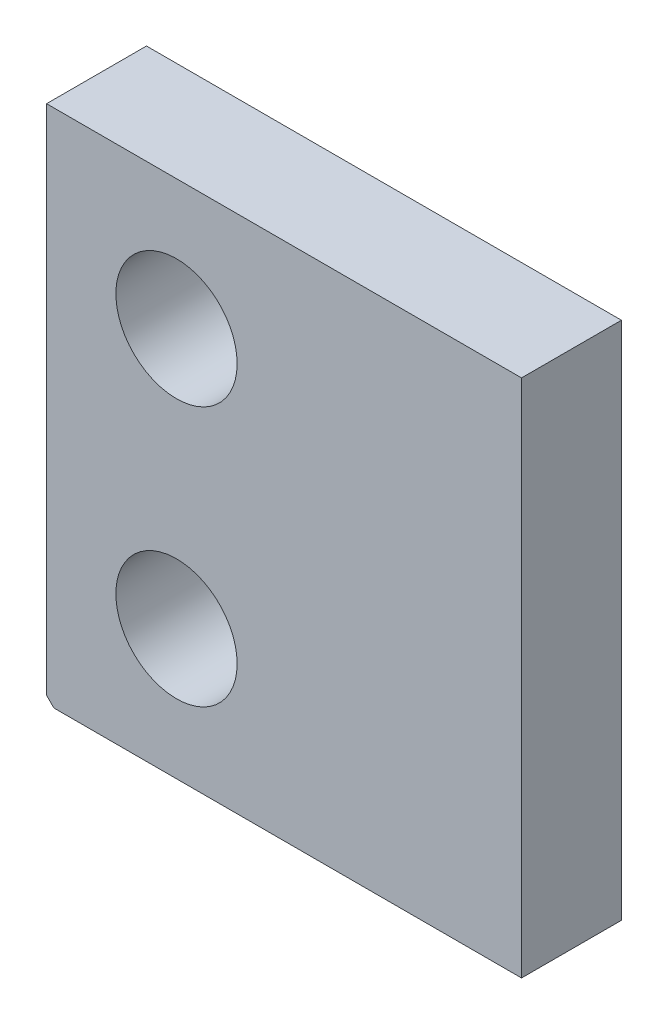
SolidWorks part; units mm, degrees
ref_plane "Front Plane" through (0, 0, 0) normal (0, 0, 1) x (1, 0, 0)
ref_plane "Top Plane" through (0, 0, 0) normal (0, 1, 0) x (1, 0, 0)
ref_plane "Right Plane" through (0, 0, 0) normal (1, 0, 0) x (0, 0, -1)
sketch "Sketch1" plane through (0, 0, 0) normal (0, 0, 1) x (1, 0, 0)
  line L1 (-16.45, -18) -> (16.45, -18)
  line L2 (-16.45, -18) -> (-16.45, 18)
  line L3 (-16.45, 18) -> (16.45, 18)
  line L4 (16.45, -18) -> (16.45, 18)
  line L5 (-16.45, -18) -> (16.45, 18) construction
  line L6 (-16.45, 18) -> (16.45, -18) construction
  point P0 (0, 0)
  dimension "D1" = 36
  dimension "D2" = 32.9
extrude "Boss-Extrude1" add sketch "Sketch1" along normal blind 6.92
hole_wizard "M8 Clearance Hole1" positions "Sketch2" profile "Sketch3" hole size "M8" standard "ANSI Metric" end condition through all
sketch "Sketch2" plane through (0, 0, 6.92) normal (0, 0, 1) x (1, 0, 0)
  point P0 (-7.45, -9)
  point P3 (-7.45, 9)
sketch "Sketch3" plane through (-7.45, -9, 6.92) normal (1, 0, 0) x (0, -1, 0)
  line L0 (0, 0) -> (0, 6.92)
  line L1 (0, 6.92) -> (4.2, 6.92)
  line L2 (4.2, 6.92) -> (4.2, 0)
  line L5 (4.2, 0) -> (0, 0)
  line L11 (0, -6.35) -> (0, 107.95) construction
  dimension "Thru Hole Dia." = 8.4
  dimension "Thru Hole Depth" = 6.92
chamfer "Chamfer1" distance 0.508 angle 45 1 edges at (-16.45, -18, 3.46)
